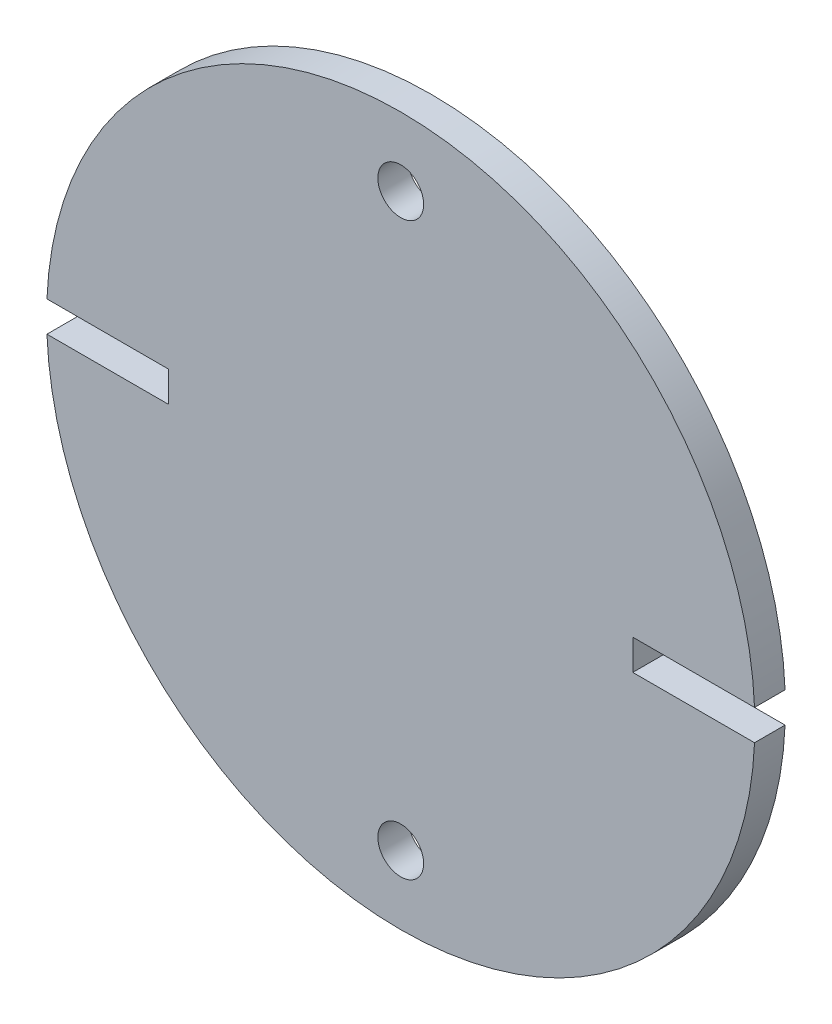
SolidWorks part; units mm, degrees
material "E-Glass Fiber"
ref_plane "Front Plane" through (0, 0, 0) normal (0, 0, 1) x (1, 0, 0)
ref_plane "Top Plane" through (0, 0, 0) normal (0, 1, 0) x (1, 0, 0)
ref_plane "Right Plane" through (0, 0, 0) normal (1, 0, 0) x (0, 0, -1)
sketch "Sketch1" plane through (0, 0, 0) normal (0, 0, 1) x (1, 0, 0)
  circle A0 centre (0, 0) radius 73.66
  dimension "D1" = 147.32
extrude "Boss-Extrude1" add sketch "Sketch1" along normal blind 6.35
sketch "Sketch2" plane through (0, 0, 0) normal (0, 0, -1) x (-1, 0, 0)
  line L0 (-76.2, 0) -> (73.66, 0) construction
  line L1 (-48.26, 0) -> (-48.26, 3.175)
  line L2 (-48.26, 3.175) -> (-76.2, 3.175)
  line L3 (-76.2, 3.175) -> (-76.2, -3.175)
  line L4 (-76.2, -3.175) -> (-48.26, -3.175)
  line L5 (-48.26, -3.175) -> (-48.26, 0)
  line L6 (0, 35.7336) -> (0, -26.6213) construction
  line L7 (48.26, -3.175) -> (48.26, 0)
  line L8 (48.26, 0) -> (48.26, 3.175)
  line L9 (76.2, -3.175) -> (48.26, -3.175)
  line L10 (76.2, 3.175) -> (76.2, -3.175)
  line L11 (48.26, 3.175) -> (76.2, 3.175)
  circle A0 centre (0, 0) radius 73.66 construction
  point P21 (-48.26, 1.5875)
  dimension "D1" = 6.35
  dimension "D2" = 27.94
  dimension "D3" = 48.26
extrude "Cut-Extrude1" cut sketch "Sketch2" against normal through all
sketch "Sketch3" plane through (0, 0, 0) normal (0, 0, -1) x (-1, 0, 0)
  line L0 (-73.93, 0) -> (73.5325, 0) construction
  line L1 (0, 73.66) -> (0, -73.66) construction
  line L3 (-38.1, 54.61) -> (38.1, 54.61)
  line L4 (-38.1, 54.61) -> (-38.1, -54.61)
  line L5 (-38.1, -54.61) -> (38.1, -54.61)
  line L6 (38.1, 54.61) -> (38.1, -54.61)
  line L7 (-38.1, 54.61) -> (38.1, -54.61) construction
  line L8 (-38.1, -54.61) -> (38.1, 54.61) construction
  arc A0 (73.5915, 3.175) -> (-73.5915, 3.175) centre (0, 0) ccw construction
  arc A1 (-73.5915, -3.175) -> (73.5915, -3.175) centre (0, 0) ccw construction
  point P11 (0, 0)
sketch "Sketch4" plane through (0, 0, 0) normal (0, 0, -1) x (-1, 0, 0)
  line L0 (47.625, 0) -> (73.5325, 0) construction
  line L2 (0, 73.66) -> (0, -73.66) construction
  line L3 (-73.93, 0) -> (38.1, 0) construction
  line L4 (0, 0) -> (38.1, 0)
  line L5 (38.1, 54.61) -> (38.1, -54.61) construction
  line L7 (0, 73.66) -> (0, -54.61) construction
  line L8 (0, -64.135) -> (0, -73.66) construction
  circle A0 centre (0, -59.3725) radius 4.7625
  circle A1 centre (0, 59.3725) radius 4.7625
  circle A2 centre (42.8625, 0) radius 4.7625
  circle A3 centre (-42.8625, 0) radius 4.7625
extrude "Cut-Extrude2" cut sketch "Sketch4" against normal through all contours A0 | A1
